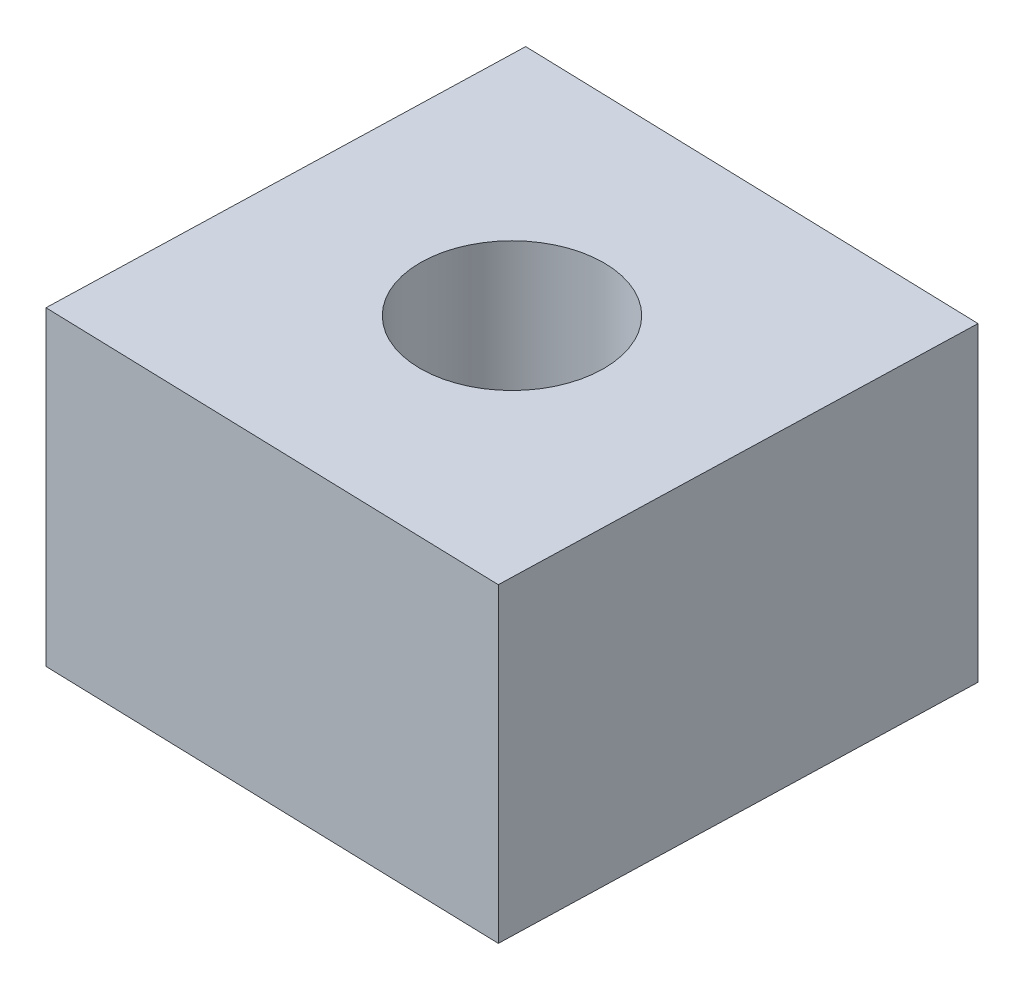
SolidWorks part; units mm, degrees
ref_plane "Front Plane" through (0, 0, 0) normal (0, 0, 1) x (1, 0, 0)
ref_plane "Top Plane" through (0, 0, 0) normal (0, 1, 0) x (1, 0, 0)
ref_plane "Right Plane" through (0, 0, 0) normal (1, 0, 0) x (0, 0, -1)
sketch "Sketch1" plane through (0, 0, 0) normal (0, 1, 0) x (1, 0, 0)
  line L6 (-3.9221, -3.6979) -> (3.6979, -3.9221)
  line L7 (3.6979, -3.9221) -> (3.9221, 3.6979)
  line L8 (3.9221, 3.6979) -> (-3.6979, 3.9221)
  line L9 (-3.6979, 3.9221) -> (-3.9221, -3.6979)
  circle A0 centre (0, 0) radius 6.35
  circle A2 centre (0, 0) radius 3.8116 construction
  circle A3 centre (0, 0) radius 1.5
  dimension "D1" = 7.62
  dimension "D2" = 3
extrude "Boss-Extrude1" add sketch "Sketch1" along normal blind 5.08
